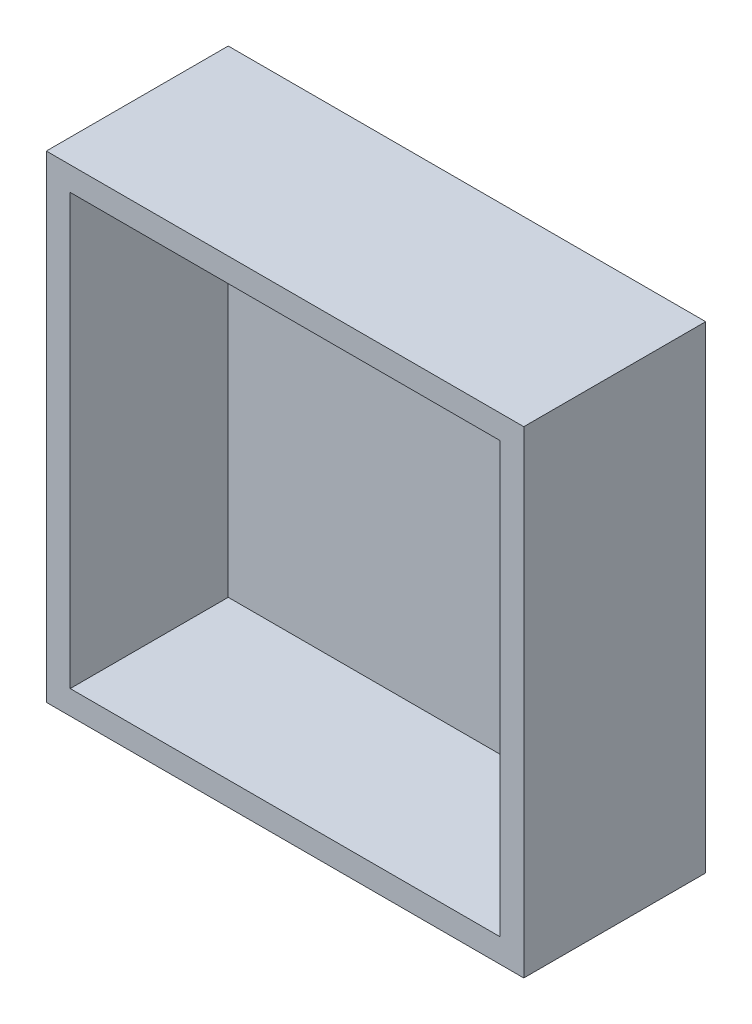
SolidWorks part; units mm, degrees
ref_plane "Front Plane" through (0, 0, 0) normal (0, 0, 1) x (1, 0, 0)
ref_plane "Top Plane" through (0, 0, 0) normal (0, 1, 0) x (1, 0, 0)
ref_plane "Right Plane" through (0, 0, 0) normal (1, 0, 0) x (0, 0, -1)
sketch "Sketch1" plane through (0, 0, 0) normal (0, 0, 1) x (1, 0, 0)
  line L1 (0, 0) -> (-200, 0)
  line L2 (0, 0) -> (0, 200)
  line L3 (0, 200) -> (-200, 200)
  line L4 (-200, 0) -> (-200, 200)
  dimension "D1" = 200
  dimension "D2" = 200
extrude "Boss-Extrude1" add sketch "Sketch1" along normal blind 76.2
sketch "Sketch2" plane through (0, 0, 76.2) normal (0, 0, 1) x (1, 0, 0)
  line L0 (0, 200) -> (-200, 200) construction
  line L1 (-190, 190) -> (-10, 190)
  line L2 (-190, 190) -> (-190, 10)
  line L3 (-190, 10) -> (-10, 10)
  line L4 (-10, 190) -> (-10, 10)
  line L5 (-200, 0) -> (0, 0) construction
  line L6 (0, 0) -> (0, 200) construction
  line L7 (-200, 200) -> (-200, 0) construction
  dimension "D1" = 10
  dimension "D2" = 10
  dimension "D3" = 10
  dimension "D4" = 10
extrude "Cut-Extrude2" cut sketch "Sketch2" against normal blind 80
sketch "Sketch3" plane through (0, 0, 0) normal (0, 0, 1) x (1, 0, 0)
  line L0 (-190, 190) -> (-10, 190)
  line L1 (-10, 190) -> (-10, 10)
  line L2 (-10, 10) -> (-190, 10)
  line L3 (-190, 10) -> (-190, 190)
extrude "Boss-Extrude2" add sketch "Sketch3" along normal blind 10
